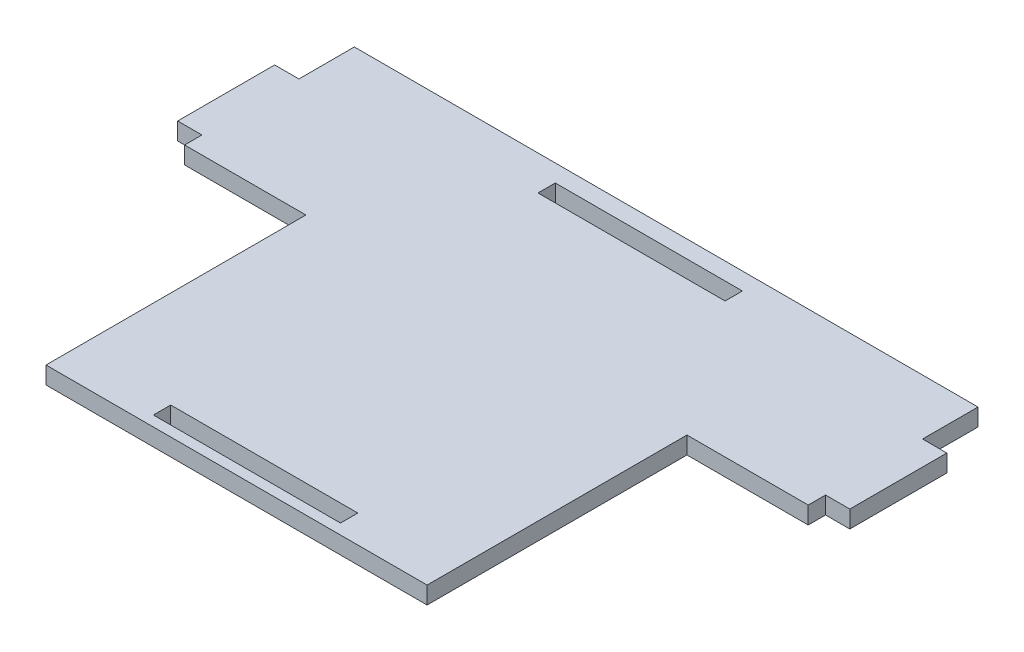
SolidWorks part; units mm, degrees
ref_plane "Front Plane" through (0, 0, 0) normal (0, 0, 1) x (1, 0, 0)
ref_plane "Top Plane" through (0, 0, 0) normal (0, 1, 0) x (1, 0, 0)
ref_plane "Right Plane" through (0, 0, 0) normal (1, 0, 0) x (0, 0, -1)
sketch "Sketch1" plane through (0, 0, 0) normal (0, 1, 0) x (1, 0, 0)
  line L0 (-90, 47) -> (-97, 47)
  line L1 (-55, -61) -> (55, -61)
  line L2 (-90, 14) -> (-90, 19)
  line L3 (-90, 63) -> (90, 63)
  line L4 (90, 14) -> (90, 19)
  line L5 (-90, 14) -> (-55, 14)
  line L7 (-97, 47) -> (-97, 19)
  line L8 (-97, 19) -> (-90, 19)
  line L9 (-90, 47) -> (-90, 63)
  line L10 (90, 14) -> (55, 14)
  line L11 (97, 19) -> (90, 19)
  line L12 (97, 47) -> (97, 19)
  line L13 (90, 47) -> (97, 47)
  line L14 (90, 47) -> (90, 63)
  line L15 (-27, 53) -> (27, 53)
  line L16 (-27, 53) -> (-27, 58)
  line L17 (-27, 58) -> (27, 58)
  line L18 (27, 53) -> (27, 58)
  line L19 (-27, 53) -> (27, 58) construction
  line L20 (-27, 58) -> (27, 53) construction
  line L30 (-55, 14) -> (-55, -61)
  line L31 (55, 14) -> (55, -61)
  line L32 (-27, -58) -> (27, -58)
  line L33 (27, -58) -> (27, -53)
  line L34 (-27, -53) -> (27, -53)
  line L35 (-27, -58) -> (-27, -53)
  point P0 (0, 0)
  point P11 (0, 55.5)
  point P13 (0, 0)
  point P23 (0, 0)
  dimension "D1" = 180
  dimension "D2" = 58
  dimension "D3" = 16
  dimension "D4" = 28
  dimension "D5" = 7
  dimension "D6" = 54
  dimension "D7" = 0
  dimension "D8" = 5
  dimension "D9" = 5
  dimension "D10" = 16
  dimension "D11" = 35
  dimension "D12" = 35
  dimension "D13" = 3
  dimension "D14" = 5
  dimension "D15" = 28
  dimension "D16" = 7
  dimension "D17" = 63
  dimension "D18" = 63
  dimension "D19" = 54
  dimension "D20" = 53
  dimension "D21" = 75
extrude "Boss-Extrude1" add sketch "Sketch1" along normal blind 5
